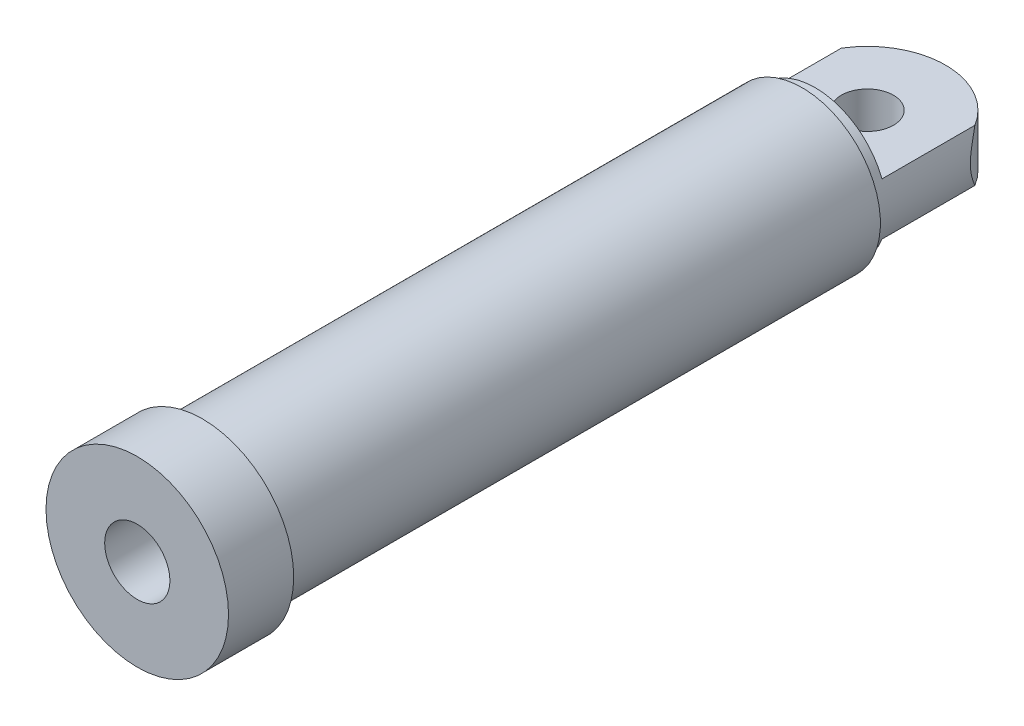
SolidWorks part; units mm, degrees
material "AISI 4340 Steel, normalized"
ref_plane "Front Plane" through (0, 0, 0) normal (0, 0, 1) x (1, 0, 0)
ref_plane "Top Plane" through (0, 0, 0) normal (0, 1, 0) x (1, 0, 0)
ref_plane "Right Plane" through (0, 0, 0) normal (1, 0, 0) x (0, 0, -1)
sketch "Sketch1" plane through (0, 0, 0) normal (0, 1, 0) x (1, 0, 0)
  line L0 (0, 0) -> (0, -560) construction
  line L1 (0, -560) -> (70, -560) construction
  line L2 (70, -560) -> (70, -510)
  line L3 (70, -510) -> (60, -510)
  line L4 (60, -510) -> (60, -40)
  line L5 (60, -40) -> (0, -40)
  line L6 (70, -560) -> (25, -560)
  line L7 (25, -560) -> (25, -480)
  line L8 (25, -480) -> (45, -480)
  line L9 (45, -480) -> (45, -60)
  line L10 (45, -60) -> (0, -60)
  line L11 (0, -60) -> (0, -40)
  circle A0 centre (0, 0) radius 20 construction
  circle A1 centre (0, 0) radius 60 construction
  dimension "D5" = 120
  dimension "D6" = 40
  dimension "D1" = 560
  dimension "D2" = 120
  dimension "D3" = 10
  dimension "D4" = 50
  dimension "D7" = 80
  dimension "D8" = 15
  dimension "D9" = 50
  dimension "D10" = 20
  dimension "D11" = 40
revolve "Revolve1" add sketch "Sketch1" angle 360 about L0
sketch "Sketch2" plane through (0, 0, 0) normal (0, 1, 0) x (1, 0, 0)
  line L0 (60, -40) -> (60, 0)
  line L1 (-60, -40) -> (-60, 0)
  line L2 (60, -40) -> (-60, -40)
  circle A0 centre (0, 0) radius 20
  circle A1 centre (0, 0) radius 20 construction
  arc A2 (60, 0) -> (-60, 0) centre (0, 0) ccw
  circle A3 centre (0, 0) radius 60 construction
extrude "Boss-Extrude1" add sketch "Sketch2" along normal mid plane 40
sketch "Sketch3" plane through (0, 0, 40) normal (0, 0, -1) x (-1, 0, 0)
  circle A0 centre (0, 0) radius 55
  circle A2 centre (0, 0) radius 63.2456
  arc A3 (56.5685, 20) -> (-56.5685, 20) centre (0, 0) ccw construction
  dimension "D1" = 5
extrude "Cut-Extrude1" cut sketch "Sketch3" along normal through all and the other way blind 10
